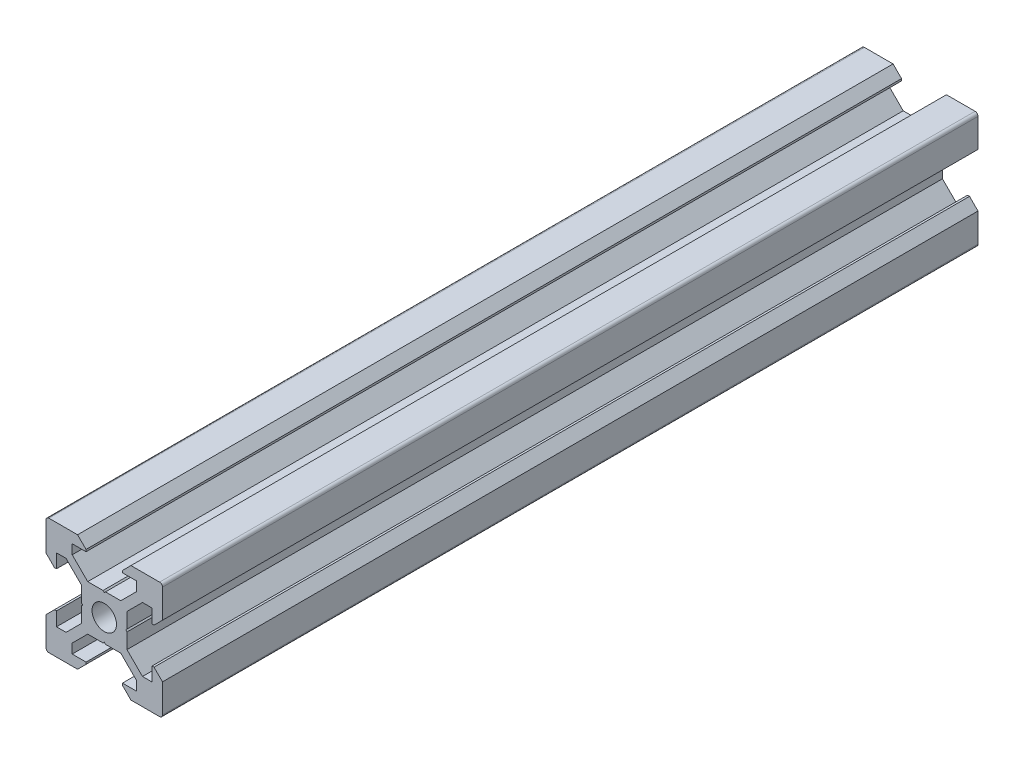
SolidWorks part; units mm, degrees
material "6061-T6 (SS)"
ref_plane "Front Plane" through (0, 0, 0) normal (0, 0, 1) x (1, 0, 0)
ref_plane "Top Plane" through (0, 0, 0) normal (0, 1, 0) x (1, 0, 0)
ref_plane "Right Plane" through (0, 0, 0) normal (1, 0, 0) x (0, 0, -1)
sketch "Sketch1" plane through (0, 0, 0) normal (0, 0, 1) x (1, 0, 0)
  line L1 (9.5, -10) -> (-9.5, -10)
  line L2 (10, -9.5) -> (10, 9.5)
  line L3 (9.5, 10) -> (-9.5, 10)
  line L4 (-10, -9.5) -> (-10, 9.5)
  line L5 (10, -10) -> (-10, 10) construction
  line L6 (10, 10) -> (-10, -10) construction
  circle A0 centre (0, 0) radius 2.1
  arc A1 (-9.5, 10) -> (-10, 9.5) centre (-9.5, 9.5) ccw
  arc A2 (10, 9.5) -> (9.5, 10) centre (9.5, 9.5) ccw
  arc A3 (9.5, -10) -> (10, -9.5) centre (9.5, -9.5) ccw
  arc A4 (-9.5, -10) -> (-10, -9.5) centre (-9.5, -9.5) cw
  point P0 (0, 0)
  line B0 (0, 0) -> (0, 10) construction
  line B1 (0, 3.69) -> (-0.21, 3.9)
  line B2 (-0.21, 3.9) -> (-2.8393, 3.9)
  line B3 (-2.8393, 3.9) -> (-5.5, 6.5607)
  line B4 (-5.5, 6.5607) -> (-5.5, 8.2)
  line B5 (-5.5, 8.2) -> (-3.125, 8.2)
  line B6 (-3.125, 8.2) -> (-3.125, 8.545)
  line B7 (-3.125, 8.545) -> (-4.58, 10)
  line B8 (-4.58, 10) -> (4.58, 10)
  line B9 (0, 0) -> (-5.9132, 5.9132) construction
  line B10 (3.125, 8.545) -> (4.58, 10)
  line B11 (3.125, 8.2) -> (3.125, 8.545)
  line B12 (5.5, 8.2) -> (3.125, 8.2)
  line B13 (5.5, 6.5607) -> (5.5, 8.2)
  line B14 (2.8393, 3.9) -> (5.5, 6.5607)
  line B15 (0.21, 3.9) -> (2.8393, 3.9)
  line B16 (0, 3.69) -> (0.21, 3.9)
  line B17 (0, 0) -> (-10, 0) construction
  line B18 (-3.69, 0) -> (-3.9, -0.21)
  line B19 (-3.9, -0.21) -> (-3.9, -2.8393)
  line B20 (-3.9, -2.8393) -> (-6.5607, -5.5)
  line B21 (-6.5607, -5.5) -> (-8.2, -5.5)
  line B22 (-8.2, -5.5) -> (-8.2, -3.125)
  line B23 (-8.2, -3.125) -> (-8.545, -3.125)
  line B24 (-8.545, -3.125) -> (-10, -4.58)
  line B25 (-10, -4.58) -> (-10, 4.58)
  line B26 (0, 0) -> (-5.9132, -5.9132) construction
  line B27 (-8.545, 3.125) -> (-10, 4.58)
  line B28 (-8.2, 3.125) -> (-8.545, 3.125)
  line B29 (-8.2, 5.5) -> (-8.2, 3.125)
  line B30 (-6.5607, 5.5) -> (-8.2, 5.5)
  line B31 (-3.9, 2.8393) -> (-6.5607, 5.5)
  line B32 (-3.9, 0.21) -> (-3.9, 2.8393)
  line B33 (-3.69, 0) -> (-3.9, 0.21)
  line B34 (0, 0) -> (0, -10) construction
  line B35 (0, -3.69) -> (0.21, -3.9)
  line B36 (0.21, -3.9) -> (2.8393, -3.9)
  line B37 (2.8393, -3.9) -> (5.5, -6.5607)
  line B38 (5.5, -6.5607) -> (5.5, -8.2)
  line B39 (5.5, -8.2) -> (3.125, -8.2)
  line B40 (3.125, -8.2) -> (3.125, -8.545)
  line B41 (3.125, -8.545) -> (4.58, -10)
  line B42 (4.58, -10) -> (-4.58, -10)
  line B43 (0, 0) -> (5.9132, -5.9132) construction
  line B44 (-3.125, -8.545) -> (-4.58, -10)
  line B45 (-3.125, -8.2) -> (-3.125, -8.545)
  line B46 (-5.5, -8.2) -> (-3.125, -8.2)
  line B47 (-5.5, -6.5607) -> (-5.5, -8.2)
  line B48 (-2.8393, -3.9) -> (-5.5, -6.5607)
  line B49 (-0.21, -3.9) -> (-2.8393, -3.9)
  line B50 (0, -3.69) -> (-0.21, -3.9)
  line B51 (0, 0) -> (10, 0) construction
  line B52 (3.69, 0) -> (3.9, 0.21)
  line B53 (3.9, 0.21) -> (3.9, 2.8393)
  line B54 (3.9, 2.8393) -> (6.5607, 5.5)
  line B55 (6.5607, 5.5) -> (8.2, 5.5)
  line B56 (8.2, 5.5) -> (8.2, 3.125)
  line B57 (8.2, 3.125) -> (8.545, 3.125)
  line B58 (8.545, 3.125) -> (10, 4.58)
  line B59 (10, 4.58) -> (10, -4.58)
  line B60 (0, 0) -> (5.9132, 5.9132) construction
  line B61 (8.545, -3.125) -> (10, -4.58)
  line B62 (8.2, -3.125) -> (8.545, -3.125)
  line B63 (8.2, -5.5) -> (8.2, -3.125)
  line B64 (6.5607, -5.5) -> (8.2, -5.5)
  line B65 (3.9, -2.8393) -> (6.5607, -5.5)
  line B66 (3.9, -0.21) -> (3.9, -2.8393)
  line B67 (3.69, 0) -> (3.9, -0.21)
  dimension "D1" = 4.2
  dimension "D3" = 0.5
  dimension "D2" = 20
sketch_block_instance "V Slot 1-4"
sketch_block "V Slot 1" parameters "D1"=10, "D2"=11, "D3"=4.3, "D4"=1.8, "D5"=0.21, "D6"=45, "D7"=9.16, "D8"=1.5, "D9"=6.25
sketch_block_instance "V Slot 1-5"
sketch_block_instance "V Slot 1-6"
sketch_block_instance "V Slot 1-7"
extrude "Boss-Extrude1" add sketch "Sketch1" along normal blind 140 contours B67 B52 B53 B54 B55 B56 B57 B58 L2 A2 L3 B10 B11 B12 B13 B14 B15 B16 B1 B2 B3 B4 B5 B6 B7 A1 L4 B27 B28 B29 B30 B31 B32 B33 B18 B19 B20 B21 B22 B23 B24 A4 L1 B44 B45 B46 B47 B48 B49
